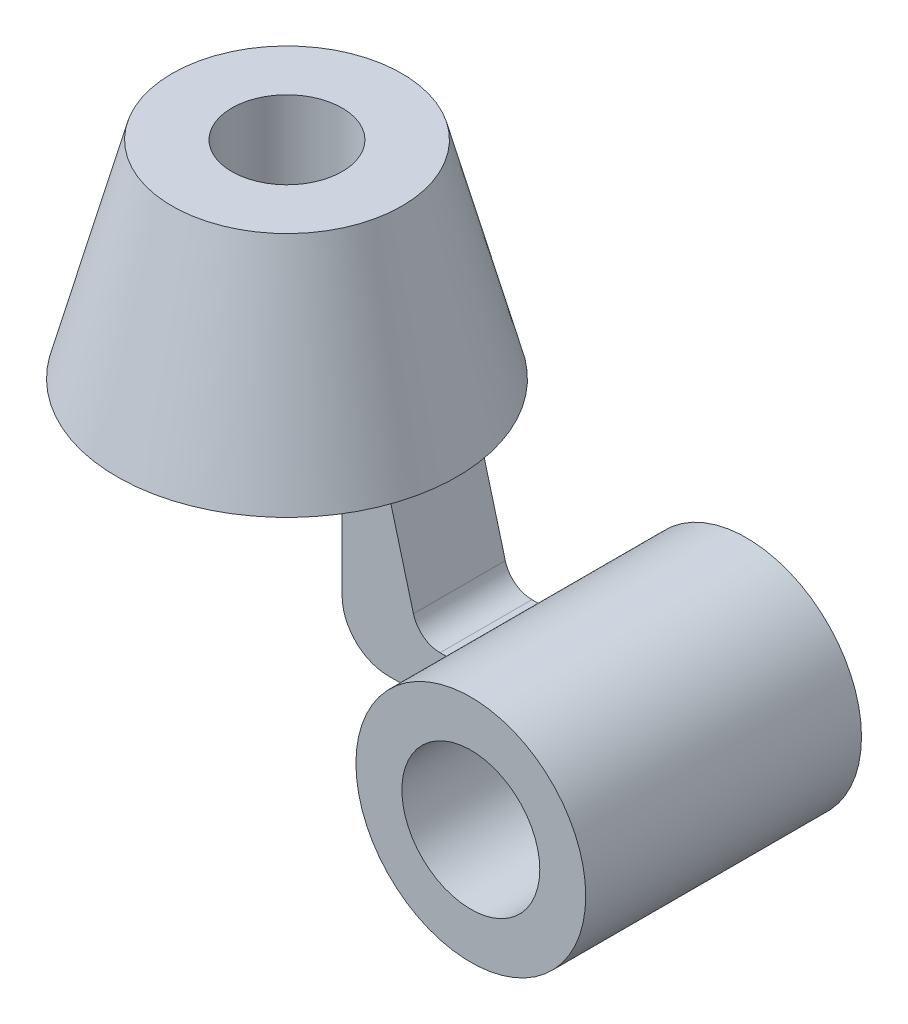
SolidWorks part; units mm, degrees
ref_plane "Front Plane" through (0, 0, 0) normal (0, 0, 1) x (1, 0, 0)
ref_plane "Top Plane" through (0, 0, 0) normal (0, 1, 0) x (1, 0, 0)
ref_plane "Right Plane" through (0, 0, 0) normal (1, 0, 0) x (0, 0, -1)
sketch "Sketch1" plane through (0, 0, 0) normal (0, 0, 1) x (1, 0, 0)
  line L0 (0, 45) -> (0, 0)
  line L1 (0, 0) -> (37, 0)
  line L2 (37, 0) -> (25, 45)
  line L3 (25, 45) -> (0, 45)
  dimension "D1" = 25
  dimension "D2" = 37
  dimension "D3" = 45
revolve "Revolve1" add sketch "Sketch1" angle 360 about L0
sketch "Sketch2" plane through (0, 45, 0) normal (0, 1, 0) x (1, 0, 0)
  circle A0 centre (0, 0) radius 12
  dimension "D1" = 24
extrude "Cut-Extrude1" cut sketch "Sketch2" against normal blind 45
sketch "Sketch3" plane through (0, 0, 0) normal (0, 0, 1) x (1, 0, 0)
  line L0 (22, 0) -> (32, 0)
  line L1 (-37, 0) -> (37, 0) construction
  line L2 (32, 0) -> (37.5071, -20.5529)
  line L3 (43.3027, -25) -> (50.5747, -25)
  line L4 (50.5747, -25) -> (50.5747, -35)
  line L5 (50.5747, -35) -> (32, -35)
  line L6 (22, -25) -> (22, 0)
  arc A0 (32, -35) -> (22, -25) centre (32, -25) cw
  arc A1 (37.5071, -20.5529) -> (43.3027, -25) centre (43.3027, -19) ccw
  point P11 (22, -35)
  dimension "D6" = 10
  dimension "D7" = 6
  dimension "D1" = 22
  dimension "D2" = 10
  dimension "D3" = 10
  dimension "D4" = 35
  dimension "D5" = 15
extrude "Boss-Extrude1" add sketch "Sketch3" along normal mid plane 20
sketch "Sketch4" plane through (0, 0, 0) normal (0, 0, 1) x (1, 0, 0)
  line L0 (32, -35) -> (50.5747, -35) construction
  line L1 (33.1002, -35) -> (109.5944, -35) construction
  circle A0 centre (70, -35) radius 15
  circle A1 centre (70, -35) radius 25
  dimension "D1" = 30
  dimension "D2" = 50
  dimension "D3" = 70
extrude "Boss-Extrude2" add sketch "Sketch4" along normal mid plane 60
